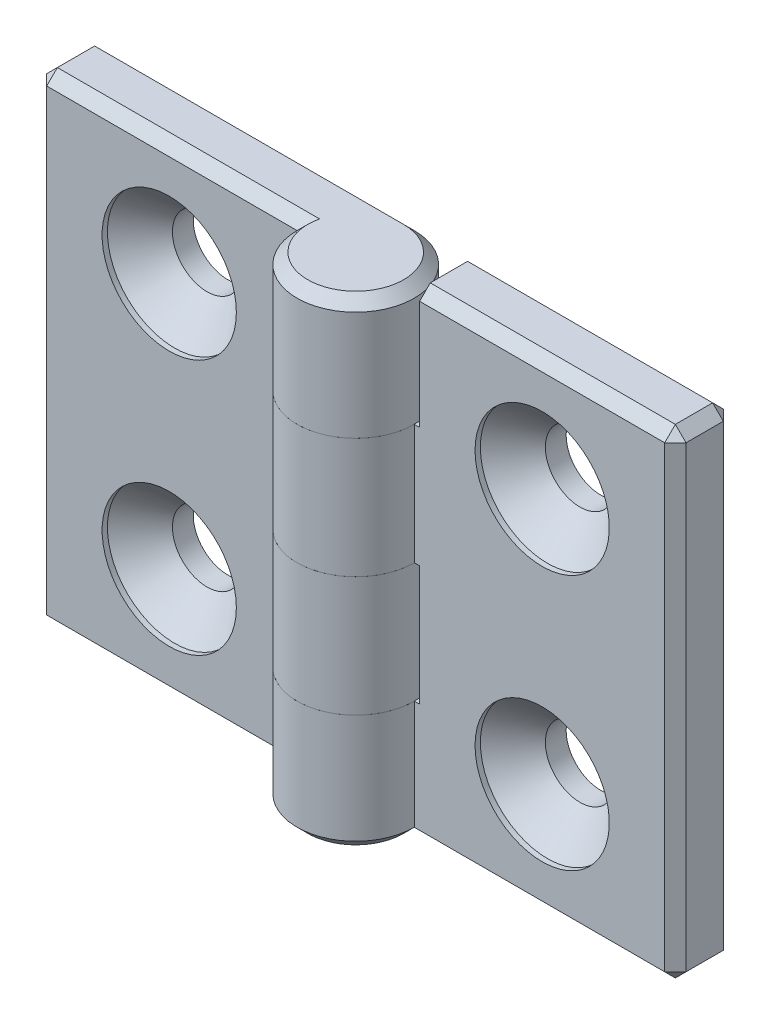
SolidWorks part; units mm, degrees
material "Нейлон"
ref_plane "Спереди" through (0, 0, 0) normal (0, 0, 1) x (1, 0, 0)
ref_plane "Сверху" through (0, 0, 0) normal (0, 1, 0) x (1, 0, 0)
ref_plane "Справа" through (0, 0, 0) normal (1, 0, 0) x (0, 0, -1)
sketch "Эскиз1" plane through (0, 0, 0) normal (0, 1, 0) x (1, 0, 0)
  line L0 (0, 5.5) -> (-30, 5.5)
  line L1 (-30, 5.5) -> (-30, 0)
  line L3 (-30, 0) -> (-5.5, 0)
  line L4 (0, 0) -> (0, 10.5526) construction
  arc A0 (-5.5, 0) -> (0, 5.5) centre (0, 0) ccw
  point P1 (0, 0)
  dimension "D1" = 60
  dimension "D2" = 5.5
extrude "Бобышка-Вытянуть1" add sketch "Эскиз1" along normal mid plane 45
sketch "Эскиз3" plane through (0, 0, 0) normal (0, 0, 1) x (1, 0, 0)
  line L0 (5.5, -22.5) -> (5.5, 22.5) construction
  line L1 (-6, 11.25) -> (5.5, 11.25)
  line L2 (-6, 11.25) -> (-6, 0)
  line L3 (-6, 0) -> (5.5, 0)
  line L4 (5.5, 11.25) -> (5.5, 0)
  line L5 (5.5, 0) -> (5.5, -11.25) construction
  line L6 (5.5, -22.5) -> (-6, -22.5)
  line L7 (5.5, -22.5) -> (5.5, -11.25)
  line L8 (5.5, -11.25) -> (-6, -11.25)
  line L9 (-6, -22.5) -> (-6, -11.25)
  line L10 (5.5, 11.25) -> (5.5, 22.5) construction
  line L11 (-5.5, 22.5) -> (-5.5, -22.5) construction
  dimension "D1" = 0.5
extrude "Вырез-Вытянуть1" cut sketch "Эскиз3" against normal through all and the other way through all
hole_wizard "Зенковка для винта с полупотайной головкой M61" positions "Эскиз4" profile "Эскиз6" countersink size "M6" standard "ISO" end condition through all
sketch "Эскиз4" plane through (0, 0, 0) normal (0, 0, 1) x (1, 0, 0)
  line L0 (-17.5, 12) -> (-17.5, -12)
  line L2 (0, 0) -> (0, 18.9001) construction
  line L3 (5.5, 0) -> (-5.5, 0) construction
  point P0 (-17.5, 12)
  point P2 (-17.5, -12)
  point P9 (-17.5, 0)
  dimension "D1" = 24
  dimension "D2" = 35
sketch "Эскиз6" plane through (-17.5, 12, 0) normal (1, 0, 0) x (0, -1, 0)
  line L0 (0, 0) -> (0, 5.5)
  line L1 (0, 5.5) -> (3.25, 5.5)
  line L2 (3.25, 5.5) -> (3.25, 3.55)
  line L3 (3.25, 3.55) -> (6.3, 0.5)
  line L4 (6.3, 0.5) -> (6.3, 0)
  line L6 (6.3, 0) -> (0, 0)
  line L7 (-3.25, 3.55) -> (-6.3, 0.5) construction
  line L11 (0, -6.35) -> (0, 107.95) construction
  dimension "Диаметр сквозного отверстия" = 6.5
  dimension "Глубина сквозного отверстия" = 5.5
  dimension "Диаметр зенковки" = 12.6
  dimension "Угол зенковки" = 90
  dimension "Утопленность" = 0.5
chamfer "Фаска1" distance 1 angle 45 9 edges at (-18, -22.5, 0) (-30, 0, 0) (-17.75, 22.5, 0) (-30, -22.5, -2.75) (-30, 22.5, -2.75) (3.8891, 22.5, 3.8891) (-15, 22.5, -5.5) (-30, 0, -5.5) (-18, -22.5, -5.5)
sketch "Угол раскрытия" plane through (0, 0, 0) normal (0, 1, 0) x (1, 0, 0)
  line L0 (0, 0) -> (0, -10)
  line L7 (0, 5.5) -> (-30, 5.5) construction
  dimension "D1" = 10
  dimension "D2" = 90
pattern_circular "Круговой массив1" count 2 over 360 about axis through (0, 0, 0) along (0, 0, 1) of bodies 106
